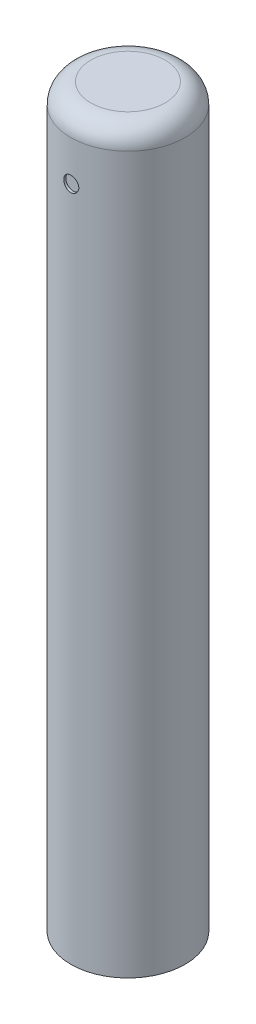
SolidWorks part; units mm, degrees
ref_plane "Front Plane" through (0, 0, 0) normal (0, 0, 1) x (1, 0, 0)
ref_plane "Top Plane" through (0, 0, 0) normal (0, 1, 0) x (1, 0, 0)
ref_plane "Right Plane" through (0, 0, 0) normal (1, 0, 0) x (0, 0, -1)
sketch "Sketch1" plane through (0, 0, 0) normal (0, 1, 0) x (1, 0, 0)
  circle A0 centre (0, 0) radius 14.5
  dimension "D1" = 29
extrude "Boss-Extrude1" add sketch "Sketch1" along normal blind 186.69
fillet "Fillet1" radius 5.08 1 edges at (0, 186.69, 14.5)
ref_plane "Plane1" through (0, 0, 14.5) normal (0, 0, 1) x (1, 0, 0)
ref_plane "Plane2" through (0, 0, -14.5) normal (0, 0, 1) x (1, 0, 0)
sketch "Sketch2" plane through (0, 0, 14.5) normal (0, 0, 1) x (1, 0, 0)
  line L0 (-14.5, 0) -> (14.5, 0) construction
  circle A0 centre (0, 171.45) radius 1.905
  point P4 (0, 0)
  dimension "D1" = 3.81
  dimension "D2" = 171.45
sketch "Sketch5" plane through (0, 0, -14.5) normal (0, 0, 1) x (1, 0, 0)
  circle A0 centre (0, 171.45) radius 1.905
  dimension "D2" = 3.81
  dimension "D1" = 171.45
extrude "Cut-Extrude4" cut sketch "Sketch5" along normal blind 0.635
extrude "Cut-Extrude5" cut sketch "Sketch2" against normal blind 0.635
